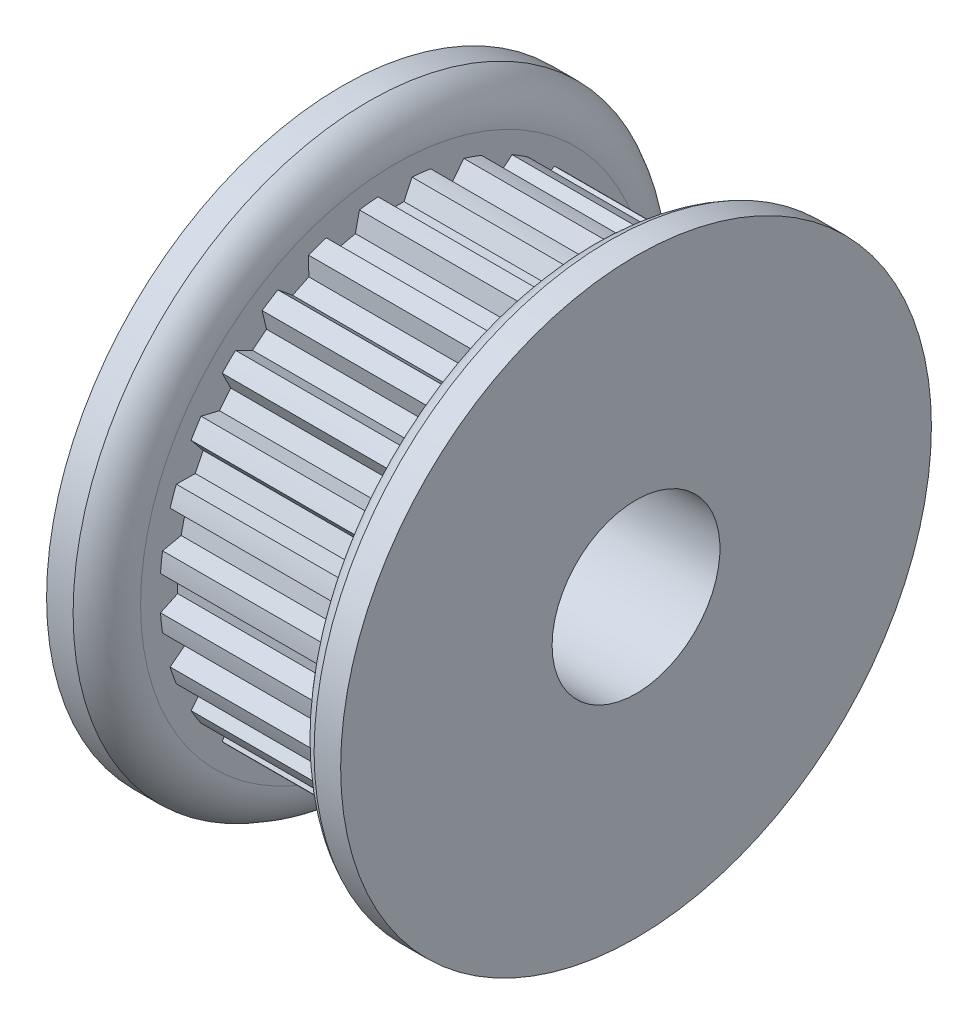
SolidWorks part; units mm, degrees
ref_plane "Front Plane" through (0, 0, 0) normal (0, 0, 1) x (1, 0, 0)
ref_plane "Top Plane" through (0, 0, 0) normal (0, 1, 0) x (1, 0, 0)
ref_plane "Right Plane" through (0, 0, 0) normal (1, 0, 0) x (0, 0, -1)
sketch "Sketch2" plane through (0, 0, 0) normal (1, 0, 0) x (0, 0, -1)
  line L3 (0, 0) -> (0, 8.2296) construction
  line L6 (0, -8.7376) -> (0, -9.0551) construction
  line L7 (-0.5715, 8.7189) -> (-0.3401, 8.2226)
  line L8 (0.5715, 8.7189) -> (0.3401, 8.2226)
  line L9 (-0.5715, 8.7189) -> (-0.6434, 8.8731)
  line L10 (0.5715, 8.7189) -> (0.6434, 8.8731)
  line L12 (-0.3401, 8.2226) -> (0.3401, 8.2226)
  line L14 (0, 8.7376) -> (0, 9.0551) construction
  line L15 (0, 0) -> (0, -1.143) construction
  circle A0 centre (0, 0) radius 9.0551 construction
  circle A1 centre (0, 0) radius 8.2296 construction
  circle A2 centre (0, 0) radius 8.7376 construction
  arc A7 (0.6434, 8.8731) -> (-0.6434, 8.8731) centre (0, 0) ccw
  point P5 (0, 8.8963)
  dimension "D3" = 0.3175
  dimension "D1" = 50
sketch "Sketch1" plane through (0, 0, 0) normal (0, 0, 1) x (1, 0, 0)
  line L0 (-8.7376, 0) -> (8.7376, 0) construction
  line L1 (-8.7376, 3.175) -> (8.7376, 3.175)
  line L2 (-8.7376, 3.175) -> (-8.7376, 8.7376)
  line L3 (-2.3876, 11.176) -> (-1.3843, 11.176)
  line L4 (-0.381, 9.0551) -> (-0.381, 9.6266)
  line L5 (-0.381, 10.1981) -> (-0.381, 9.0551) construction
  line L6 (-0.381, 9.0551) -> (6.731, 9.0551)
  line L7 (6.731, 9.0551) -> (6.731, 9.6266)
  line L8 (6.731, 9.0551) -> (8.7376, 9.0551) construction
  line L9 (7.7343, 11.176) -> (8.7376, 11.176)
  line L10 (8.7376, 11.176) -> (8.7376, 3.175)
  line L11 (7.7343, 9.0551) -> (7.7343, 11.176) construction
  line L12 (-5.5626, 8.7376) -> (-5.5626, 3.175) construction
  line L13 (-2.3876, 11.176) -> (-2.3876, 8.7376)
  line L14 (-2.3876, 8.7376) -> (-8.7376, 8.7376)
  arc A0 (6.731, 9.6266) -> (7.7343, 11.176) centre (8.429, 9.6266) cw
  arc A1 (-0.381, 9.6266) -> (-1.3843, 11.176) centre (-2.079, 9.6266) ccw
  dimension "Bore Size" = 6.35
  dimension "Overall Width" = 17.4752
  dimension "Inside Width" = 7.112
  dimension "OD" = 22.352
  dimension "D2" = 18.1102
  dimension "D3" = 1.143
  dimension "D4" = 0.5715
  dimension "Outside Width" = 11.1252
revolve "Revolve1" add sketch "Sketch1" angle 360 mid plane about L0
sketch "Sketch4" plane through (-0.381, 0, 0) normal (1, 0, 0) x (0, 0, -1)
  circle A0 centre (0, 0) radius 8.8963
  circle A2 centre (0, 0) radius 9.0551
  circle A3 centre (0, 0) radius 9.0551 construction
extrude "Cut-Extrude2" cut sketch "Sketch4" along normal up to surface (7.112 mm away) up to face at (6.731, 0, 9.0551)
sketch "Sketch3" plane through (-0.381, 0, 0) normal (1, 0, 0) x (0, 0, -1)
  line L2 (-0.5715, 8.7189) -> (-0.3401, 8.2226) construction
  line L3 (-0.3401, 8.2226) -> (0.3401, 8.2226) construction
  line L4 (0.5715, 8.7189) -> (0.3401, 8.2226) construction
  line L5 (-0.6434, 8.8731) -> (-0.3401, 8.2226)
  line L6 (-0.3401, 8.2226) -> (0.3401, 8.2226)
  line L7 (0.6434, 8.8731) -> (0.3401, 8.2226)
  arc A1 (0.6434, 8.8731) -> (-0.6434, 8.8731) centre (0, 0) ccw construction
  arc A2 (0.6434, 8.8731) -> (-0.6434, 8.8731) centre (0, 0) ccw
extrude "Cut-Extrude1" cut sketch "Sketch3" along normal up to surface (7.112 mm away) up to face at (6.731, 0, 9.6266)
pattern_circular "CirPattern1" count 28 over 360 about axis through (0, 0, 0) along (1, 0, 0) of "Cut-Extrude1"
sketch "Sketch5" plane through (0, 0, 0) normal (0, 0, 1) x (1, 0, 0)
  line L1 (6.731, 9.6266) -> (6.731, -9.6266) construction
  point P0 (6.731, 0)
sketch "Sketch6" plane through (-8.7376, 0, 0) normal (-1, 0, 0) x (0, 0, 1)
  circle A0 centre (0, 0) radius 8.7376
  circle A1 centre (0, 0) radius 8.7376 construction
extrude "Cut-Extrude3" cut sketch "Sketch6" against normal up to surface (6.35 mm away) up to face at (-2.3876, 0, 8.7376)
equation "\"D3@Sketch2\" = (\"hs@Sketch2\"-\"ht@Sketch2\")/2"
equation "\"D2@Sketch1\" = \"PD@Sketch2\""
equation "\"D3@Sketch1\" = \"hs@Sketch2\""
equation "\"D4@Sketch1\" = \"D3@Sketch1\"/2"
